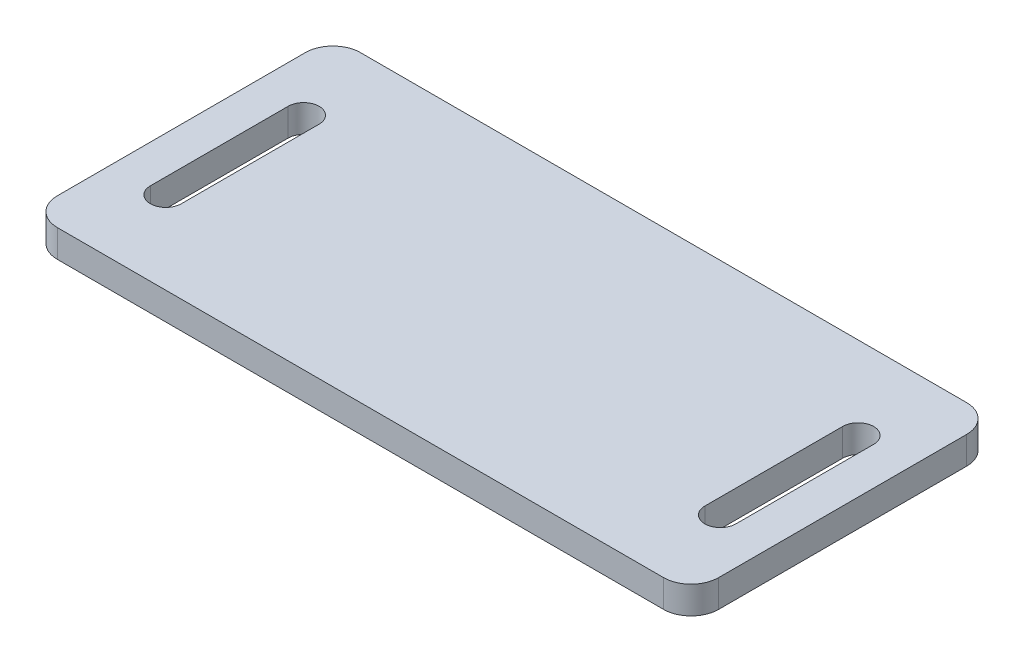
SolidWorks part; units mm, degrees
ref_plane "Front Plane" through (0, 0, 0) normal (0, 0, 1) x (1, 0, 0)
ref_plane "Top Plane" through (0, 0, 0) normal (0, 1, 0) x (1, 0, 0)
ref_plane "Right Plane" through (0, 0, 0) normal (1, 0, 0) x (0, 0, -1)
sketch "Sketch1" plane through (0, 0, 0) normal (0, 1, 0) x (1, 0, 0)
  line L0 (-40.25, 10) -> (-40.25, -10) construction
  line L1 (-44, -22) -> (44, -22)
  line L2 (-48, -18) -> (-48, 18)
  line L3 (-44, 22) -> (44, 22)
  line L4 (48, -18) -> (48, 18)
  line L5 (-48, -22) -> (48, 22) construction
  line L6 (-48, 22) -> (48, -22) construction
  line L7 (-38, 10) -> (-38, -10)
  line L8 (-42.5, 10) -> (-42.5, -10)
  line L9 (40.25, 10) -> (40.25, -10) construction
  line L10 (42.5, 10) -> (42.5, -10)
  line L11 (38, 10) -> (38, -10)
  arc A0 (44, 22) -> (48, 18) centre (44, 18) cw
  arc A1 (44, -22) -> (48, -18) centre (44, -18) ccw
  arc A2 (-44, -22) -> (-48, -18) centre (-44, -18) cw
  arc A3 (-48, 18) -> (-44, 22) centre (-44, 18) cw
  arc A4 (-38, 10) -> (-42.5, 10) centre (-40.25, 10) ccw
  arc A5 (-42.5, -10) -> (-38, -10) centre (-40.25, -10) ccw
  arc A6 (42.5, 10) -> (38, 10) centre (40.25, 10) ccw
  arc A7 (38, -10) -> (42.5, -10) centre (40.25, -10) ccw
  point P0 (0, 0)
  point P20 (-40.25, 0)
  point P26 (40.25, 0)
  dimension "D3" = 4
  dimension "D5" = 2.25
  dimension "D1" = 44
  dimension "D2" = 96
  dimension "D4" = 80.5
  dimension "D6" = 20
  dimension "D7" = 40.25
extrude "Boss-Extrude1" add sketch "Sketch1" along normal mid plane 4
equation "\"D7@Sketch1\"=\"D4@Sketch1\"/2"
